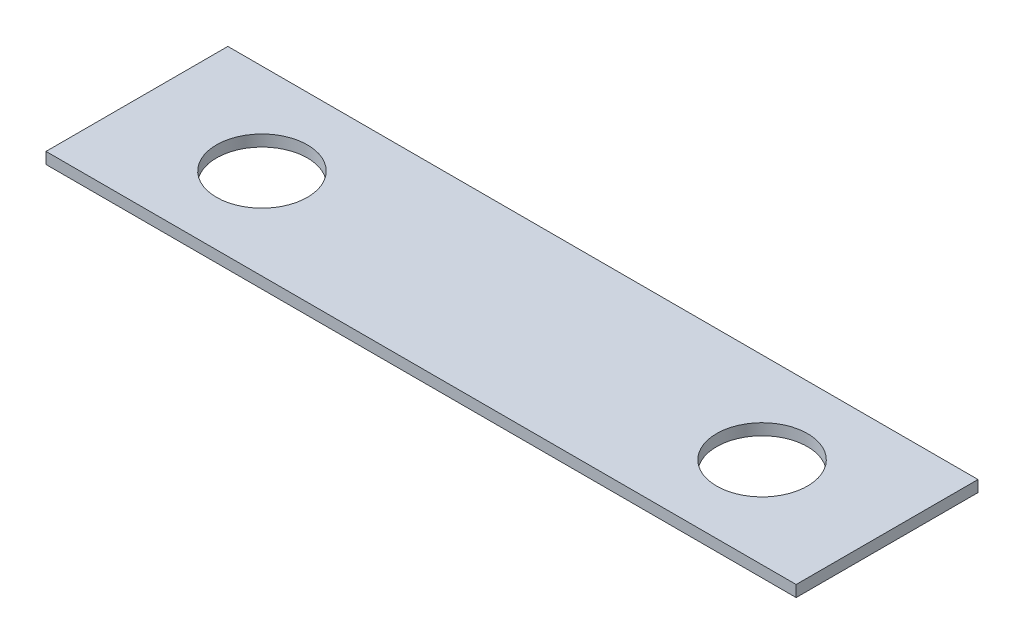
SolidWorks part; units mm, degrees
material "Brass"
ref_plane "Front Plane" through (0, 0, 0) normal (0, 0, 1) x (1, 0, 0)
ref_plane "Top Plane" through (0, 0, 0) normal (0, 1, 0) x (1, 0, 0)
ref_plane "Right Plane" through (0, 0, 0) normal (1, 0, 0) x (0, 0, -1)
sketch "Sketch1" plane through (0, 0, 0) normal (0, 1, 0) x (1, 0, 0)
  line L0 (-44.2539, 0) -> (44.2539, 0) construction
  line L1 (-16.5, -4) -> (16.5, -4)
  line L2 (-16.5, -4) -> (-16.5, 4)
  line L3 (-16.5, 4) -> (16.5, 4)
  line L4 (16.5, -4) -> (16.5, 4)
  line L5 (-16.5, -4) -> (16.5, 4) construction
  line L6 (-16.5, 4) -> (16.5, -4) construction
  line L7 (0, -44.7868) -> (0, 44.7868) construction
  circle A0 centre (-11, 0) radius 2
  circle A1 centre (11, 0) radius 2
  point P0 (0, 0)
  dimension "D3" = 4
  dimension "D4" = 22
  dimension "D5" = 11
  dimension "D1" = 8
  dimension "D2" = 33
extrude "Boss-Extrude1" add sketch "Sketch1" along normal blind 0.5 contours L1 L4 L3 L2
